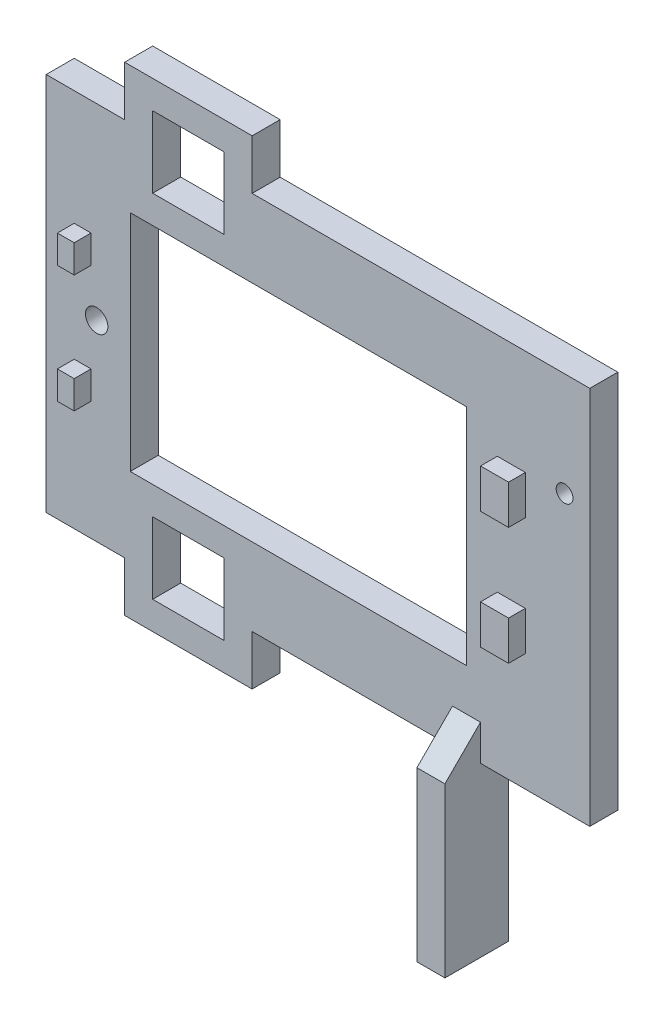
SolidWorks part; units mm, degrees
ref_plane "Front Plane" through (0, 0, 0) normal (0, 0, 1) x (1, 0, 0)
ref_plane "Top Plane" through (0, 0, 0) normal (0, 1, 0) x (1, 0, 0)
ref_plane "Right Plane" through (0, 0, 0) normal (1, 0, 0) x (0, 0, -1)
sketch "Sketch1" plane through (0, 0, 0) normal (0, 0, 1) x (1, 0, 0)
  line L1 (0, 0) -> (-97, 0)
  line L2 (0, 0) -> (0, 67.7)
  line L3 (0, 67.7) -> (-97, 67.7)
  line L4 (-97, 0) -> (-97, 67.7)
  dimension "D1" = 97
  dimension "D2" = 67.7
extrude "Boss-Extrude1" add sketch "Sketch1" along normal blind 5
sketch "Sketch2" plane through (0, 0, 5) normal (0, 0, 1) x (1, 0, 0)
  line L0 (-97, 0) -> (0, 0) construction
  line L1 (-97, 67.7) -> (-97, 0) construction
  line L2 (-82, 53.85) -> (-22, 53.85)
  line L3 (-82, 53.85) -> (-82, 13.85)
  line L4 (-82, 13.85) -> (-22, 13.85)
  line L5 (-22, 53.85) -> (-22, 13.85)
  line L6 (0, 0) -> (0, 67.7) construction
  circle A0 centre (-88, 34.2) radius 2
  circle A1 centre (-4.5, 49.2) radius 1.5
  point P14 (-97, 33.85)
  point P16 (-82, 33.85)
  dimension "D1" = 4
  dimension "D4" = 3
  dimension "D7" = 34.2
  dimension "D8" = 15
  dimension "D2" = 60
  dimension "D3" = 40
  dimension "D5" = 15
  dimension "D6" = 9
  dimension "D9" = 4.5
extrude "Cut-Extrude1" cut sketch "Sketch2" against normal through all
sketch "Sketch3" plane through (0, 0, 5) normal (0, 0, 1) x (1, 0, 0)
  line L1 (-92, 47.2) -> (-89, 47.2)
  line L2 (-92, 47.2) -> (-92, 42.2)
  line L3 (-92, 42.2) -> (-89, 42.2)
  line L4 (-89, 47.2) -> (-89, 42.2)
  line L5 (-92, 26.2) -> (-89, 26.2)
  line L6 (-92, 26.2) -> (-92, 21.2)
  line L7 (-92, 21.2) -> (-89, 21.2)
  line L8 (-89, 26.2) -> (-89, 21.2)
  line L9 (-16.5, 48.95) -> (-11.5, 48.95)
  line L10 (-16.5, 48.95) -> (-16.5, 41.95)
  line L11 (-16.5, 41.95) -> (-11.5, 41.95)
  line L12 (-11.5, 48.95) -> (-11.5, 41.95)
  line L13 (-16.5, 27.95) -> (-11.5, 27.95)
  line L14 (-16.5, 27.95) -> (-16.5, 20.95)
  line L15 (-16.5, 20.95) -> (-11.5, 20.95)
  line L16 (-11.5, 27.95) -> (-11.5, 20.95)
  circle A0 centre (-88, 34.2) radius 2 construction
  circle A1 centre (-4.5, 49.2) radius 1.5 construction
  dimension "D1" = 5
  dimension "D2" = 3
  dimension "D3" = 8
  dimension "D4" = 16
  dimension "D5" = 1
  dimension "D6" = 7
  dimension "D7" = 5
  dimension "D8" = 0.25
  dimension "D9" = 14
  dimension "D10" = 7
extrude "Boss-Extrude2" add sketch "Sketch3" along normal blind 3
sketch "Sketch4" plane through (0, 0, 0) normal (0, 0, -1) x (-1, 0, 0)
  line L1 (65.25, 58.85) -> (78, 58.85)
  line L2 (65.25, 58.85) -> (65.25, 71.6)
  line L3 (65.25, 71.6) -> (78, 71.6)
  line L4 (78, 58.85) -> (78, 71.6)
  line L5 (22, 53.85) -> (82, 53.85) construction
  line L6 (65.25, 8.85) -> (78, 8.85)
  line L7 (65.25, 8.85) -> (65.25, -3.9)
  line L8 (65.25, -3.9) -> (78, -3.9)
  line L9 (78, 8.85) -> (78, -3.9)
  line L10 (82, 13.85) -> (22, 13.85) construction
  circle A0 centre (88, 34.2) radius 2 construction
  dimension "D1" = 10
  dimension "D2" = 12.75
  dimension "D3" = 12.75
  dimension "D4" = 5
  dimension "D5" = 5
sketch "Sketch7" plane through (0, 0, 0) normal (0, -1, 0) x (1, 0, 0)
  line L0 (-97, 0) -> (0, 0) construction
  line L1 (-19.5, 11.35) -> (-24.5, 11.35)
  line L2 (-19.5, 11.35) -> (-19.5, 0)
  line L3 (-19.5, 0) -> (-24.5, 0)
  line L4 (-24.5, 11.35) -> (-24.5, 0)
  line L7 (0, 5) -> (0, 0) construction
  line L8 (-97, 5) -> (0, 5) construction
  point P12 (-22, 0)
  dimension "D1" = 22
  dimension "D2" = 5
  dimension "D3" = 6.35
extrude "Boss-Extrude4" add sketch "Sketch7" along normal blind 30
sketch "Sketch8" plane through (-19.5, 0, 0) normal (1, 0, 0) x (0, 0, -1)
  line L0 (-11.35, 0) -> (-5, 0)
  line L1 (-5, 0) -> (-5, 6.35)
  line L2 (-5, 0) -> (-5, 67.7) construction
  line L3 (-5, 6.35) -> (-11.35, 0)
  dimension "D1" = 45
extrude "Boss-Extrude5" add sketch "Sketch8" against normal up to surface (5 mm away) up to face at (-24.5, -15, 6.04)
extrude "Cut-Extrude2" cut sketch "Sketch4" against normal through all
sketch "Sketch10" plane through (0, 0, 0) normal (0, 0, -1) x (-1, 0, 0)
  line L0 (83, 0) -> (83, -8.9)
  line L1 (97, 0) -> (78, 0) construction
  line L2 (83, -8.9) -> (60.25, -8.9)
  line L3 (60.25, -8.9) -> (60.25, 0)
  line L4 (65.25, 0) -> (24.5, 0) construction
  line L5 (60.25, 0) -> (65.25, 0)
  line L6 (65.25, 0) -> (65.25, -3.9)
  line L7 (65.25, -3.9) -> (78, -3.9)
  line L8 (78, -3.9) -> (78, 0)
  line L9 (78, 0) -> (83, 0)
  line L10 (83, 67.7) -> (78, 67.7)
  line L11 (78, 67.7) -> (97, 67.7) construction
  line L12 (78, 67.7) -> (78, 71.6)
  line L13 (78, 71.6) -> (65.25, 71.6)
  line L14 (65.25, 71.6) -> (65.25, 67.7)
  line L15 (65.25, 67.7) -> (60.25, 67.7)
  line L16 (0, 67.7) -> (65.25, 67.7) construction
  line L17 (60.25, 67.7) -> (60.25, 76.6)
  line L18 (60.25, 76.6) -> (83, 76.6)
  line L19 (83, 76.6) -> (83, 67.7)
  dimension "D1" = 12.75
  dimension "D2" = 5
  dimension "D3" = 5
  dimension "D4" = 5
extrude "Boss-Extrude6" add sketch "Sketch10" against normal up to surface (5 mm away) up to face at (-53.4375, 26.1812, 5)
